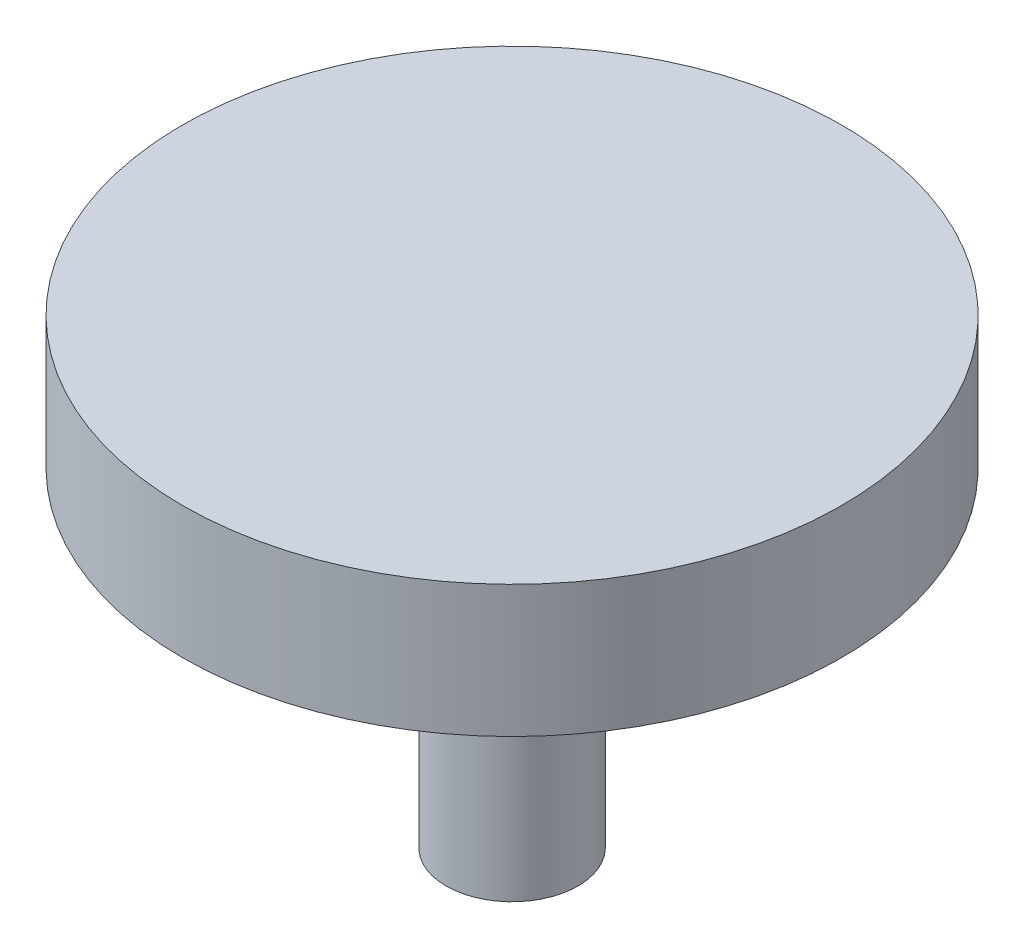
SolidWorks part; units mm, degrees
ref_plane "Front Plane" through (0, 0, 0) normal (0, 0, 1) x (1, 0, 0)
ref_plane "Top Plane" through (0, 0, 0) normal (0, 1, 0) x (1, 0, 0)
ref_plane "Right Plane" through (0, 0, 0) normal (1, 0, 0) x (0, 0, -1)
sketch "Sketch1" plane through (0, 0, 0) normal (0, 1, 0) x (1, 0, 0)
  circle A1 centre (0, 0) radius 25
extrude "Boss-Extrude1" add sketch "Sketch1" along normal blind 10
sketch "Sketch2" plane through (0, 0, 0) normal (0, 1, 0) x (1, 0, 0)
  circle A0 centre (0, 0) radius 5
  dimension "D1" = 10
extrude "Boss-Extrude2" add sketch "Sketch2" against normal blind 25
